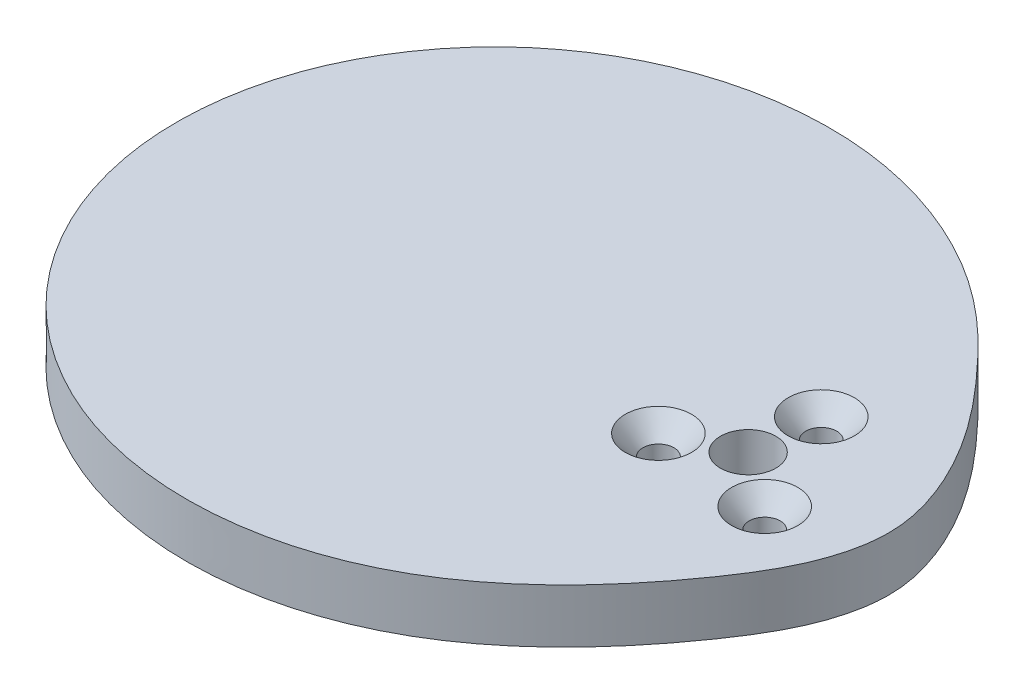
SolidWorks part; units mm, degrees
material "AISI 303 Stainless"
ref_plane "Front Plane" through (0, 0, 0) normal (0, 0, 1) x (1, 0, 0)
ref_plane "Top Plane" through (0, 0, 0) normal (0, 1, 0) x (1, 0, 0)
ref_plane "Right Plane" through (0, 0, 0) normal (1, 0, 0) x (0, 0, -1)
other "Configuration Table"
sketch "Generated Profile" plane through (0, 0, 0) normal (0, 1, 0) x (1, 0, 0)
  line L0 (0, 0) -> (25.4, 0) construction
  arc A0 (16.51, 0) -> (16.5074, 0.2882) centre (-1.1956, -0.0156) ccw
  arc A1 (16.5074, 0.2882) -> (16.4999, 0.5764) centre (-0.0271, -0.0004) ccw
  arc A2 (16.4999, 0.5764) -> (16.4873, 0.8647) centre (-0.0737, -0.0021) ccw
  arc A3 (16.4873, 0.8647) -> (16.4697, 1.1532) centre (-0.1437, -0.0058) ccw
  arc A4 (16.4697, 1.1532) -> (16.447, 1.4419) centre (-0.2374, -0.0123) ccw
  arc A5 (16.447, 1.4419) -> (16.4193, 1.7309) centre (-0.3551, -0.0226) ccw
  arc A6 (16.4193, 1.7309) -> (16.3866, 2.0202) centre (-0.4972, -0.0375) ccw
  arc A7 (16.3866, 2.0202) -> (16.3488, 2.3099) centre (-0.6642, -0.0579) ccw
  arc A8 (16.3488, 2.3099) -> (16.3059, 2.6) centre (-0.8568, -0.0847) ccw
  arc A9 (16.3059, 2.6) -> (16.2579, 2.8906) centre (-1.0754, -0.1189) ccw
  arc A10 (16.2579, 2.8906) -> (16.2049, 3.1817) centre (-1.3211, -0.1616) ccw
  arc A11 (16.2049, 3.1817) -> (16.1468, 3.4735) centre (-1.5945, -0.2138) ccw
  arc A12 (16.1468, 3.4735) -> (16.0835, 3.7658) centre (-1.8967, -0.2766) ccw
  arc A13 (16.0835, 3.7658) -> (16.0151, 4.0589) centre (-2.2288, -0.3513) ccw
  arc A14 (16.0151, 4.0589) -> (15.9416, 4.3528) centre (-2.592, -0.4391) ccw
  arc A15 (15.9416, 4.3528) -> (15.863, 4.6474) centre (-2.9877, -0.5415) ccw
  arc A16 (15.863, 4.6474) -> (15.7792, 4.9429) centre (-3.4174, -0.6598) ccw
  arc A17 (15.7792, 4.9429) -> (15.6903, 5.2394) centre (-3.8827, -0.7956) ccw
  arc A18 (15.6903, 5.2394) -> (15.5961, 5.5368) centre (-4.3854, -0.9506) ccw
  arc A19 (15.5961, 5.5368) -> (15.4968, 5.8352) centre (-4.9275, -1.1266) ccw
  arc A20 (15.4968, 5.8352) -> (15.3923, 6.1348) centre (-5.5111, -1.3256) ccw
  arc A21 (15.3923, 6.1348) -> (15.2826, 6.4355) centre (-6.1385, -1.5495) ccw
  arc A22 (15.2826, 6.4355) -> (15.1677, 6.7373) centre (-6.8121, -1.8006) ccw
  arc A23 (15.1677, 6.7373) -> (15.0476, 7.0405) centre (-7.5347, -2.0813) ccw
  arc A24 (15.0476, 7.0405) -> (14.9223, 7.3449) centre (-8.3091, -2.3941) ccw
  arc A25 (14.9223, 7.3449) -> (14.7918, 7.6508) centre (-9.1382, -2.7417) ccw
  arc A26 (14.7918, 7.6508) -> (14.6561, 7.958) centre (-10.0253, -3.127) ccw
  arc A27 (14.6561, 7.958) -> (14.5152, 8.2667) centre (-10.9736, -3.5529) ccw
  arc A28 (14.5152, 8.2667) -> (14.3691, 8.577) centre (-11.9865, -4.0226) ccw
  arc A29 (14.3691, 8.577) -> (14.2179, 8.8889) centre (-13.0674, -4.5394) ccw
  arc A30 (14.2179, 8.8889) -> (14.0614, 9.2024) centre (-14.2199, -5.1066) ccw
  arc A31 (14.0614, 9.2024) -> (13.8998, 9.5176) centre (-15.4473, -5.7275) ccw
  arc A32 (13.8998, 9.5176) -> (13.7331, 9.8345) centre (-16.7527, -6.4056) ccw
  arc A33 (13.7331, 9.8345) -> (13.5612, 10.1532) centre (-18.1389, -7.1441) ccw
  arc A34 (13.5612, 10.1532) -> (13.3843, 10.4738) centre (-19.6082, -7.9458) ccw
  arc A35 (13.3843, 10.4738) -> (13.2023, 10.7963) centre (-21.1622, -8.8133) ccw
  arc A36 (13.2023, 10.7963) -> (13.0152, 11.1207) centre (-22.8013, -9.7486) ccw
  arc A37 (13.0152, 11.1207) -> (12.8231, 11.4471) centre (-24.5248, -10.7528) ccw
  arc A38 (12.8231, 11.4471) -> (12.626, 11.7755) centre (-26.3302, -11.826) ccw
  arc A39 (12.626, 11.7755) -> (12.424, 12.1059) centre (-28.213, -12.9666) ccw
  arc A40 (12.424, 12.1059) -> (12.217, 12.4384) centre (-30.1663, -14.1717) ccw
  arc A41 (12.217, 12.4384) -> (12.0052, 12.773) centre (-32.1801, -15.436) ccw
  arc A42 (12.0052, 12.773) -> (11.7885, 13.1098) centre (-34.2413, -16.7518) ccw
  arc A43 (11.7885, 13.1098) -> (11.567, 13.4486) centre (-36.3329, -18.1087) ccw
  arc A44 (11.567, 13.4486) -> (11.3406, 13.7896) centre (-38.4346, -19.4932) ccw
  arc A45 (11.3406, 13.7896) -> (11.1095, 14.1328) centre (-40.5219, -20.8888) ccw
  arc A46 (11.1095, 14.1328) -> (10.8736, 14.4781) centre (-42.5671, -22.2759) ccw
  arc A47 (10.8736, 14.4781) -> (10.633, 14.8256) centre (-44.5394, -23.6323) ccw
  arc A48 (10.633, 14.8256) -> (10.3877, 15.1753) centre (-46.4062, -24.9334) ccw
  arc A49 (10.3877, 15.1753) -> (10.1377, 15.5271) centre (-48.1344, -26.1537) ccw
  arc A50 (10.1377, 15.5271) -> (9.8829, 15.881) centre (-49.6916, -27.2675) ccw
  arc A51 (9.8829, 15.881) -> (9.6235, 16.2371) centre (-51.0484, -28.25) ccw
  arc A52 (9.6235, 16.2371) -> (9.3593, 16.5952) centre (-52.1797, -29.0794) ccw
  arc A53 (9.3593, 16.5952) -> (9.0903, 16.9554) centre (-53.0666, -29.7375) ccw
  arc A54 (9.0903, 16.9554) -> (8.8165, 17.3177) centre (-53.6976, -30.2113) ccw
  arc A55 (8.8165, 17.3177) -> (8.5379, 17.6819) centre (-54.0689, -30.4935) ccw
  arc A56 (8.5379, 17.6819) -> (8.2544, 18.0481) centre (-54.1853, -30.5829) ccw
  arc A57 (8.2544, 18.0481) -> (7.9659, 18.4163) centre (-54.0587, -30.4842) ccw
  arc A58 (7.9659, 18.4163) -> (7.6724, 18.7863) centre (-53.708, -30.2075) ccw
  arc A59 (7.6724, 18.7863) -> (7.3737, 19.1582) centre (-53.1569, -29.7675) ccw
  arc A60 (7.3737, 19.1582) -> (7.0697, 19.5319) centre (-52.4327, -29.182) ccw
  arc A61 (7.0697, 19.5319) -> (6.7603, 19.9073) centre (-51.5645, -28.4712) ccw
  arc A62 (6.7603, 19.9073) -> (6.4454, 20.2844) centre (-50.5819, -27.656) ccw
  arc A63 (6.4454, 20.2844) -> (6.1249, 20.6631) centre (-49.5132, -26.7575) ccw
  arc A64 (6.1249, 20.6631) -> (5.7985, 21.0433) centre (-48.3852, -25.796) ccw
  arc A65 (5.7985, 21.0433) -> (5.4661, 21.4251) centre (-47.2216, -24.7901) ccw
  arc A66 (5.4661, 21.4251) -> (5.1274, 21.8083) centre (-46.0436, -23.7567) ccw
  arc A67 (5.1274, 21.8083) -> (4.7824, 22.1927) centre (-44.8688, -22.7106) ccw
  arc A68 (4.7824, 22.1927) -> (4.4307, 22.5785) centre (-43.7119, -21.6643) ccw
  arc A69 (4.4307, 22.5785) -> (4.0722, 22.9654) centre (-42.5848, -20.6285) ccw
  arc A70 (4.0722, 22.9654) -> (3.7066, 23.3533) centre (-41.4966, -19.6117) ccw
  arc A71 (3.7066, 23.3533) -> (3.3337, 23.7422) centre (-40.454, -18.6207) ccw
  arc A72 (3.3337, 23.7422) -> (2.9533, 24.1319) centre (-39.4618, -17.6608) ccw
  arc A73 (2.9533, 24.1319) -> (2.565, 24.5222) centre (-38.5231, -16.7358) ccw
  arc A74 (2.565, 24.5222) -> (2.1686, 24.9132) centre (-37.6395, -15.8485) ccw
  arc A75 (2.1686, 24.9132) -> (1.7638, 25.3045) centre (-36.8115, -15.0007) ccw
  arc A76 (1.7638, 25.3045) -> (1.3505, 25.696) centre (-36.0388, -14.1934) ccw
  arc A77 (1.3505, 25.696) -> (0.9282, 26.0876) centre (-35.3203, -13.4268) ccw
  arc A78 (0.9282, 26.0876) -> (0.4967, 26.479) centre (-34.6543, -12.7009) ccw
  arc A79 (0.4967, 26.479) -> (0.0558, 26.87) centre (-34.0389, -12.015) ccw
  arc A80 (0.0558, 26.87) -> (-0.3948, 27.2605) centre (-33.4719, -11.3683) ccw
  arc A81 (-0.3948, 27.2605) -> (-0.8554, 27.6501) centre (-32.9508, -10.7597) ccw
  arc A82 (-0.8554, 27.6501) -> (-1.3263, 28.0387) centre (-32.473, -10.188) ccw
  arc A83 (-1.3263, 28.0387) -> (-1.8077, 28.4259) centre (-32.0361, -9.6518) ccw
  arc A84 (-1.8077, 28.4259) -> (-2.2999, 28.8114) centre (-31.6373, -9.1495) ccw
  arc A85 (-2.2999, 28.8114) -> (-2.8032, 29.195) centre (-31.2743, -8.6798) ccw
  arc A86 (-2.8032, 29.195) -> (-3.3177, 29.5763) centre (-30.9445, -8.2411) ccw
  arc A87 (-3.3177, 29.5763) -> (-3.8437, 29.955) centre (-30.6455, -7.8319) ccw
  arc A88 (-3.8437, 29.955) -> (-4.3815, 30.3306) centre (-30.375, -7.4506) ccw
  arc A89 (-4.3815, 30.3306) -> (-4.9312, 30.7029) centre (-30.1309, -7.0958) ccw
  arc A90 (-4.9312, 30.7029) -> (-5.493, 31.0715) centre (-29.911, -6.7659) ccw
  arc A91 (-5.493, 31.0715) -> (-6.0672, 31.4358) centre (-29.7134, -6.4597) ccw
  arc A92 (-6.0672, 31.4358) -> (-6.6538, 31.7956) centre (-29.5361, -6.1757) ccw
  arc A93 (-6.6538, 31.7956) -> (-7.253, 32.1503) centre (-29.3775, -5.9126) ccw
  arc A94 (-7.253, 32.1503) -> (-7.865, 32.4994) centre (-29.2359, -5.669) ccw
  arc A95 (-7.865, 32.4994) -> (-8.4898, 32.8426) centre (-29.1098, -5.4437) ccw
  arc A96 (-8.4898, 32.8426) -> (-9.1276, 33.1792) centre (-28.9976, -5.2355) ccw
  arc A97 (-9.1276, 33.1792) -> (-9.7784, 33.5089) centre (-28.8982, -5.0433) ccw
  arc A98 (-9.7784, 33.5089) -> (-10.4423, 33.8311) centre (-28.8102, -4.8659) ccw
  arc A99 (-10.4423, 33.8311) -> (-11.1193, 34.1451) centre (-28.7324, -4.7022) ccw
  arc A100 (-11.1193, 34.1451) -> (-11.8093, 34.4506) centre (-28.664, -4.5512) ccw
  arc A101 (-11.8093, 34.4506) -> (-12.5124, 34.747) centre (-28.6038, -4.4119) ccw
  arc A102 (-12.5124, 34.747) -> (-13.2285, 35.0336) centre (-28.551, -4.2834) ccw
  arc A103 (-13.2285, 35.0336) -> (-13.9575, 35.31) centre (-28.5047, -4.1647) ccw
  arc A104 (-13.9575, 35.31) -> (-14.6994, 35.5755) centre (-28.4642, -4.055) ccw
  arc A105 (-14.6994, 35.5755) -> (-15.4539, 35.8296) centre (-28.429, -3.9534) ccw
  arc A106 (-15.4539, 35.8296) -> (-16.221, 36.0716) centre (-28.3982, -3.8591) ccw
  arc A107 (-16.221, 36.0716) -> (-17.0005, 36.301) centre (-28.3714, -3.7714) ccw
  arc A108 (-17.0005, 36.301) -> (-17.7921, 36.5172) centre (-28.3482, -3.6895) ccw
  arc A109 (-17.7921, 36.5172) -> (-18.5956, 36.7196) centre (-28.328, -3.6127) ccw
  arc A110 (-18.5956, 36.7196) -> (-19.4107, 36.9076) centre (-28.3106, -3.5405) ccw
  arc A111 (-19.4107, 36.9076) -> (-20.2371, 37.0806) centre (-28.2955, -3.472) ccw
  arc A112 (-20.2371, 37.0806) -> (-21.0745, 37.2381) centre (-28.2826, -3.4069) ccw
  arc A113 (-21.0745, 37.2381) -> (-21.9226, 37.3794) centre (-28.2715, -3.3445) ccw
  arc A114 (-21.9226, 37.3794) -> (-22.7809, 37.5039) centre (-28.2621, -3.2843) ccw
  arc A115 (-22.7809, 37.5039) -> (-23.649, 37.6112) centre (-28.2543, -3.2258) ccw
  arc A116 (-23.649, 37.6112) -> (-24.5265, 37.7006) centre (-28.2478, -3.1686) ccw
  arc A117 (-24.5265, 37.7006) -> (-25.4129, 37.7716) centre (-28.2427, -3.1123) ccw
  arc A118 (-25.4129, 37.7716) -> (-26.3078, 37.8237) centre (-28.2388, -3.0565) ccw
  arc A119 (-26.3078, 37.8237) -> (-27.2105, 37.8564) centre (-28.2362, -3.0008) ccw
  arc A120 (-27.2105, 37.8564) -> (-28.1205, 37.8691) centre (-28.2348, -2.9449) ccw
  arc A121 (-28.1205, 37.8691) -> (-29.0373, 37.8613) centre (-28.2346, -2.8887) ccw
  arc A122 (-29.0373, 37.8613) -> (-29.9602, 37.8327) centre (-28.2358, -2.8317) ccw
  arc A123 (-29.9602, 37.8327) -> (-30.8886, 37.7827) centre (-28.2382, -2.7738) ccw
  arc A124 (-30.8886, 37.7827) -> (-31.8218, 37.7109) centre (-28.2421, -2.7149) ccw
  arc A125 (-31.8218, 37.7109) -> (-32.7592, 37.6169) centre (-28.2474, -2.6548) ccw
  arc A126 (-32.7592, 37.6169) -> (-33.7001, 37.5003) centre (-28.2543, -2.5933) ccw
  arc A127 (-33.7001, 37.5003) -> (-34.6437, 37.3607) centre (-28.2628, -2.5304) ccw
  arc A128 (-34.6437, 37.3607) -> (-35.5892, 37.1979) centre (-28.2731, -2.466) ccw
  arc A129 (-35.5892, 37.1979) -> (-36.536, 37.0115) centre (-28.2853, -2.4001) ccw
  arc A130 (-36.536, 37.0115) -> (-37.4833, 36.8013) centre (-28.2994, -2.3327) ccw
  arc A131 (-37.4833, 36.8013) -> (-38.4302, 36.5669) centre (-28.3156, -2.2638) ccw
  arc A132 (-38.4302, 36.5669) -> (-39.3759, 36.3081) centre (-28.3339, -2.1934) ccw
  arc A133 (-39.3759, 36.3081) -> (-40.3196, 36.0249) centre (-28.3545, -2.1217) ccw
  arc A134 (-40.3196, 36.0249) -> (-41.2605, 35.7169) centre (-28.3774, -2.0487) ccw
  arc A135 (-41.2605, 35.7169) -> (-42.1977, 35.384) centre (-28.4027, -1.9745) ccw
  arc A136 (-42.1977, 35.384) -> (-43.1303, 35.0263) centre (-28.4305, -1.8993) ccw
  arc A137 (-43.1303, 35.0263) -> (-44.0575, 34.6435) centre (-28.4608, -1.8233) ccw
  arc A138 (-44.0575, 34.6435) -> (-44.9784, 34.2357) centre (-28.4936, -1.7465) ccw
  arc A139 (-44.9784, 34.2357) -> (-45.8921, 33.8029) centre (-28.529, -1.6692) ccw
  arc A140 (-45.8921, 33.8029) -> (-46.7977, 33.345) centre (-28.567, -1.5915) ccw
  arc A141 (-46.7977, 33.345) -> (-47.6944, 32.8623) centre (-28.6076, -1.5138) ccw
  arc A142 (-47.6944, 32.8623) -> (-48.5812, 32.3547) centre (-28.6507, -1.4361) ccw
  arc A143 (-48.5812, 32.3547) -> (-49.4572, 31.8224) centre (-28.6964, -1.3587) ccw
  arc A144 (-49.4572, 31.8224) -> (-50.3216, 31.2656) centre (-28.7445, -1.2818) ccw
  arc A145 (-50.3216, 31.2656) -> (-51.1735, 30.6844) centre (-28.795, -1.2057) ccw
  arc A146 (-51.1735, 30.6844) -> (-52.012, 30.0792) centre (-28.8477, -1.1305) ccw
  arc A147 (-52.012, 30.0792) -> (-52.8362, 29.4502) centre (-28.9026, -1.0565) ccw
  arc A148 (-52.8362, 29.4502) -> (-53.6452, 28.7978) centre (-28.9596, -0.984) ccw
  arc A149 (-53.6452, 28.7978) -> (-54.4383, 28.1221) centre (-29.0183, -0.913) ccw
  arc A150 (-54.4383, 28.1221) -> (-55.2145, 27.4238) centre (-29.0788, -0.8439) ccw
  arc A151 (-55.2145, 27.4238) -> (-55.973, 26.703) centre (-29.1409, -0.7769) ccw
  arc A152 (-55.973, 26.703) -> (-56.7131, 25.9604) centre (-29.2042, -0.712) ccw
  arc A153 (-56.7131, 25.9604) -> (-57.4338, 25.1963) centre (-29.2686, -0.6496) ccw
  arc A154 (-57.4338, 25.1963) -> (-58.1344, 24.4114) centre (-29.3339, -0.5896) ccw
  arc A155 (-58.1344, 24.4114) -> (-58.8142, 23.606) centre (-29.3998, -0.5324) ccw
  arc A156 (-58.8142, 23.606) -> (-59.4724, 22.7808) centre (-29.4661, -0.478) ccw
  arc A157 (-59.4724, 22.7808) -> (-60.1083, 21.9363) centre (-29.5325, -0.4266) ccw
  arc A158 (-60.1083, 21.9363) -> (-60.7212, 21.0733) centre (-29.5987, -0.3781) ccw
  arc A159 (-60.7212, 21.0733) -> (-61.3103, 20.1923) centre (-29.6645, -0.3328) ccw
  arc A160 (-61.3103, 20.1923) -> (-61.8751, 19.2941) centre (-29.7295, -0.2906) ccw
  arc A161 (-61.8751, 19.2941) -> (-62.4149, 18.3792) centre (-29.7936, -0.2516) ccw
  arc A162 (-62.4149, 18.3792) -> (-62.929, 17.4486) centre (-29.8563, -0.2157) ccw
  arc A163 (-62.929, 17.4486) -> (-63.417, 16.5028) centre (-29.9175, -0.1831) ccw
  arc A164 (-63.417, 16.5028) -> (-63.8783, 15.5427) centre (-29.9768, -0.1535) ccw
  arc A165 (-63.8783, 15.5427) -> (-64.3123, 14.569) centre (-30.0339, -0.1271) ccw
  arc A166 (-64.3123, 14.569) -> (-64.7185, 13.5827) centre (-30.0886, -0.1036) ccw
  arc A167 (-64.7185, 13.5827) -> (-65.0966, 12.5845) centre (-30.1407, -0.083) ccw
  arc A168 (-65.0966, 12.5845) -> (-65.446, 11.5752) centre (-30.1898, -0.0652) ccw
  arc A169 (-65.446, 11.5752) -> (-65.7664, 10.5557) centre (-30.2358, -0.05) ccw
  arc A170 (-65.7664, 10.5557) -> (-66.0573, 9.5269) centre (-30.2783, -0.0373) ccw
  arc A171 (-66.0573, 9.5269) -> (-66.3186, 8.4898) centre (-30.3172, -0.0269) ccw
  arc A172 (-66.3186, 8.4898) -> (-66.5498, 7.4451) centre (-30.3524, -0.0186) ccw
  arc A173 (-66.5498, 7.4451) -> (-66.7507, 6.3938) centre (-30.3835, -0.0122) ccw
  arc A174 (-66.7507, 6.3938) -> (-66.9211, 5.3369) centre (-30.4105, -0.0074) ccw
  arc A175 (-66.9211, 5.3369) -> (-67.0608, 4.2752) centre (-30.4332, -0.0041) ccw
  arc A176 (-67.0608, 4.2752) -> (-67.1696, 3.2097) centre (-30.4515, -0.0019) ccw
  arc A177 (-67.1696, 3.2097) -> (-67.2475, 2.1414) centre (-30.4653, -0.0007) ccw
  arc A178 (-67.2475, 2.1414) -> (-67.2942, 1.0712) centre (-30.4746, -0.0001) ccw
  arc A179 (-67.2942, 1.0712) -> (-67.31, 0) centre (-29.3336, -0.025) ccw
  arc A180 (-67.31, 0) -> (-67.2942, -1.0712) centre (-29.3336, 0.025) ccw
  arc A181 (-67.2942, -1.0712) -> (-67.2475, -2.1414) centre (-30.4746, 0.0001) ccw
  arc A182 (-67.2475, -2.1414) -> (-67.1696, -3.2097) centre (-30.4653, 0.0007) ccw
  arc A183 (-67.1696, -3.2097) -> (-67.0608, -4.2752) centre (-30.4515, 0.0019) ccw
  arc A184 (-67.0608, -4.2752) -> (-66.9211, -5.3369) centre (-30.4332, 0.0041) ccw
  arc A185 (-66.9211, -5.3369) -> (-66.7507, -6.3938) centre (-30.4105, 0.0074) ccw
  arc A186 (-66.7507, -6.3938) -> (-66.5498, -7.4451) centre (-30.3835, 0.0122) ccw
  arc A187 (-66.5498, -7.4451) -> (-66.3186, -8.4898) centre (-30.3524, 0.0186) ccw
  arc A188 (-66.3186, -8.4898) -> (-66.0573, -9.5269) centre (-30.3172, 0.0269) ccw
  arc A189 (-66.0573, -9.5269) -> (-65.7664, -10.5557) centre (-30.2783, 0.0373) ccw
  arc A190 (-65.7664, -10.5557) -> (-65.446, -11.5752) centre (-30.2358, 0.05) ccw
  arc A191 (-65.446, -11.5752) -> (-65.0966, -12.5845) centre (-30.1898, 0.0652) ccw
  arc A192 (-65.0966, -12.5845) -> (-64.7185, -13.5827) centre (-30.1407, 0.083) ccw
  arc A193 (-64.7185, -13.5827) -> (-64.3123, -14.569) centre (-30.0886, 0.1036) ccw
  arc A194 (-64.3123, -14.569) -> (-63.8783, -15.5427) centre (-30.0339, 0.1271) ccw
  arc A195 (-63.8783, -15.5427) -> (-63.417, -16.5028) centre (-29.9768, 0.1535) ccw
  arc A196 (-63.417, -16.5028) -> (-62.929, -17.4486) centre (-29.9175, 0.1831) ccw
  arc A197 (-62.929, -17.4486) -> (-62.4149, -18.3792) centre (-29.8563, 0.2157) ccw
  arc A198 (-62.4149, -18.3792) -> (-61.8751, -19.2941) centre (-29.7936, 0.2516) ccw
  arc A199 (-61.8751, -19.2941) -> (-61.3103, -20.1923) centre (-29.7295, 0.2906) ccw
  arc A200 (-61.3103, -20.1923) -> (-60.7212, -21.0733) centre (-29.6645, 0.3328) ccw
  arc A201 (-60.7212, -21.0733) -> (-60.1083, -21.9363) centre (-29.5987, 0.3781) ccw
  arc A202 (-60.1083, -21.9363) -> (-59.4724, -22.7808) centre (-29.5325, 0.4266) ccw
  arc A203 (-59.4724, -22.7808) -> (-58.8142, -23.606) centre (-29.4661, 0.478) ccw
  arc A204 (-58.8142, -23.606) -> (-58.1344, -24.4114) centre (-29.3998, 0.5324) ccw
  arc A205 (-58.1344, -24.4114) -> (-57.4338, -25.1963) centre (-29.3339, 0.5896) ccw
  arc A206 (-57.4338, -25.1963) -> (-56.7131, -25.9604) centre (-29.2686, 0.6496) ccw
  arc A207 (-56.7131, -25.9604) -> (-55.973, -26.703) centre (-29.2042, 0.712) ccw
  arc A208 (-55.973, -26.703) -> (-55.2145, -27.4238) centre (-29.1409, 0.7769) ccw
  arc A209 (-55.2145, -27.4238) -> (-54.4383, -28.1221) centre (-29.0788, 0.8439) ccw
  arc A210 (-54.4383, -28.1221) -> (-53.6452, -28.7978) centre (-29.0183, 0.913) ccw
  arc A211 (-53.6452, -28.7978) -> (-52.8362, -29.4502) centre (-28.9596, 0.984) ccw
  arc A212 (-52.8362, -29.4502) -> (-52.012, -30.0792) centre (-28.9026, 1.0565) ccw
  arc A213 (-52.012, -30.0792) -> (-51.1735, -30.6844) centre (-28.8477, 1.1305) ccw
  arc A214 (-51.1735, -30.6844) -> (-50.3216, -31.2656) centre (-28.795, 1.2057) ccw
  arc A215 (-50.3216, -31.2656) -> (-49.4572, -31.8224) centre (-28.7445, 1.2818) ccw
  arc A216 (-49.4572, -31.8224) -> (-48.5812, -32.3547) centre (-28.6964, 1.3587) ccw
  arc A217 (-48.5812, -32.3547) -> (-47.6944, -32.8623) centre (-28.6507, 1.4361) ccw
  arc A218 (-47.6944, -32.8623) -> (-46.7977, -33.345) centre (-28.6076, 1.5138) ccw
  arc A219 (-46.7977, -33.345) -> (-45.8921, -33.8029) centre (-28.567, 1.5915) ccw
  arc A220 (-45.8921, -33.8029) -> (-44.9784, -34.2357) centre (-28.529, 1.6692) ccw
  arc A221 (-44.9784, -34.2357) -> (-44.0575, -34.6435) centre (-28.4936, 1.7465) ccw
  arc A222 (-44.0575, -34.6435) -> (-43.1303, -35.0263) centre (-28.4608, 1.8233) ccw
  arc A223 (-43.1303, -35.0263) -> (-42.1977, -35.384) centre (-28.4305, 1.8993) ccw
  arc A224 (-42.1977, -35.384) -> (-41.2605, -35.7169) centre (-28.4027, 1.9745) ccw
  arc A225 (-41.2605, -35.7169) -> (-40.3196, -36.0249) centre (-28.3774, 2.0487) ccw
  arc A226 (-40.3196, -36.0249) -> (-39.3759, -36.3081) centre (-28.3545, 2.1217) ccw
  arc A227 (-39.3759, -36.3081) -> (-38.4302, -36.5669) centre (-28.3339, 2.1934) ccw
  arc A228 (-38.4302, -36.5669) -> (-37.4833, -36.8013) centre (-28.3156, 2.2638) ccw
  arc A229 (-37.4833, -36.8013) -> (-36.536, -37.0115) centre (-28.2994, 2.3327) ccw
  arc A230 (-36.536, -37.0115) -> (-35.5892, -37.1979) centre (-28.2853, 2.4001) ccw
  arc A231 (-35.5892, -37.1979) -> (-34.6437, -37.3607) centre (-28.2731, 2.466) ccw
  arc A232 (-34.6437, -37.3607) -> (-33.7001, -37.5003) centre (-28.2628, 2.5304) ccw
  arc A233 (-33.7001, -37.5003) -> (-32.7592, -37.6169) centre (-28.2543, 2.5933) ccw
  arc A234 (-32.7592, -37.6169) -> (-31.8218, -37.7109) centre (-28.2474, 2.6548) ccw
  arc A235 (-31.8218, -37.7109) -> (-30.8886, -37.7827) centre (-28.2421, 2.7149) ccw
  arc A236 (-30.8886, -37.7827) -> (-29.9602, -37.8327) centre (-28.2382, 2.7738) ccw
  arc A237 (-29.9602, -37.8327) -> (-29.0373, -37.8613) centre (-28.2358, 2.8317) ccw
  arc A238 (-29.0373, -37.8613) -> (-28.1205, -37.8691) centre (-28.2346, 2.8887) ccw
  arc A239 (-28.1205, -37.8691) -> (-27.2105, -37.8564) centre (-28.2348, 2.9449) ccw
  arc A240 (-27.2105, -37.8564) -> (-26.3078, -37.8237) centre (-28.2362, 3.0008) ccw
  arc A241 (-26.3078, -37.8237) -> (-25.4129, -37.7716) centre (-28.2388, 3.0565) ccw
  arc A242 (-25.4129, -37.7716) -> (-24.5265, -37.7006) centre (-28.2427, 3.1123) ccw
  arc A243 (-24.5265, -37.7006) -> (-23.649, -37.6112) centre (-28.2478, 3.1686) ccw
  arc A244 (-23.649, -37.6112) -> (-22.7809, -37.5039) centre (-28.2543, 3.2258) ccw
  arc A245 (-22.7809, -37.5039) -> (-21.9226, -37.3794) centre (-28.2621, 3.2843) ccw
  arc A246 (-21.9226, -37.3794) -> (-21.0745, -37.2381) centre (-28.2715, 3.3445) ccw
  arc A247 (-21.0745, -37.2381) -> (-20.2371, -37.0806) centre (-28.2826, 3.4069) ccw
  arc A248 (-20.2371, -37.0806) -> (-19.4107, -36.9076) centre (-28.2955, 3.472) ccw
  arc A249 (-19.4107, -36.9076) -> (-18.5956, -36.7196) centre (-28.3106, 3.5405) ccw
  arc A250 (-18.5956, -36.7196) -> (-17.7921, -36.5172) centre (-28.328, 3.6127) ccw
  arc A251 (-17.7921, -36.5172) -> (-17.0005, -36.301) centre (-28.3482, 3.6895) ccw
  arc A252 (-17.0005, -36.301) -> (-16.221, -36.0716) centre (-28.3714, 3.7714) ccw
  arc A253 (-16.221, -36.0716) -> (-15.4539, -35.8296) centre (-28.3982, 3.8591) ccw
  arc A254 (-15.4539, -35.8296) -> (-14.6994, -35.5755) centre (-28.429, 3.9534) ccw
  arc A255 (-14.6994, -35.5755) -> (-13.9575, -35.31) centre (-28.4642, 4.055) ccw
  arc A256 (-13.9575, -35.31) -> (-13.2285, -35.0336) centre (-28.5047, 4.1647) ccw
  arc A257 (-13.2285, -35.0336) -> (-12.5124, -34.747) centre (-28.551, 4.2834) ccw
  arc A258 (-12.5124, -34.747) -> (-11.8093, -34.4506) centre (-28.6038, 4.4119) ccw
  arc A259 (-11.8093, -34.4506) -> (-11.1193, -34.1451) centre (-28.664, 4.5512) ccw
  arc A260 (-11.1193, -34.1451) -> (-10.4423, -33.8311) centre (-28.7324, 4.7022) ccw
  arc A261 (-10.4423, -33.8311) -> (-9.7784, -33.5089) centre (-28.8102, 4.8659) ccw
  arc A262 (-9.7784, -33.5089) -> (-9.1276, -33.1792) centre (-28.8982, 5.0433) ccw
  arc A263 (-9.1276, -33.1792) -> (-8.4898, -32.8426) centre (-28.9976, 5.2355) ccw
  arc A264 (-8.4898, -32.8426) -> (-7.865, -32.4994) centre (-29.1098, 5.4437) ccw
  arc A265 (-7.865, -32.4994) -> (-7.253, -32.1503) centre (-29.2359, 5.669) ccw
  arc A266 (-7.253, -32.1503) -> (-6.6538, -31.7956) centre (-29.3775, 5.9126) ccw
  arc A267 (-6.6538, -31.7956) -> (-6.0672, -31.4358) centre (-29.5361, 6.1757) ccw
  arc A268 (-6.0672, -31.4358) -> (-5.493, -31.0715) centre (-29.7134, 6.4597) ccw
  arc A269 (-5.493, -31.0715) -> (-4.9312, -30.7029) centre (-29.911, 6.7659) ccw
  arc A270 (-4.9312, -30.7029) -> (-4.3815, -30.3306) centre (-30.1309, 7.0958) ccw
  arc A271 (-4.3815, -30.3306) -> (-3.8437, -29.955) centre (-30.375, 7.4506) ccw
  arc A272 (-3.8437, -29.955) -> (-3.3177, -29.5763) centre (-30.6455, 7.8319) ccw
  arc A273 (-3.3177, -29.5763) -> (-2.8032, -29.195) centre (-30.9445, 8.2411) ccw
  arc A274 (-2.8032, -29.195) -> (-2.2999, -28.8114) centre (-31.2743, 8.6798) ccw
  arc A275 (-2.2999, -28.8114) -> (-1.8077, -28.4259) centre (-31.6373, 9.1495) ccw
  arc A276 (-1.8077, -28.4259) -> (-1.3263, -28.0387) centre (-32.0361, 9.6518) ccw
  arc A277 (-1.3263, -28.0387) -> (-0.8554, -27.6501) centre (-32.473, 10.188) ccw
  arc A278 (-0.8554, -27.6501) -> (-0.3948, -27.2605) centre (-32.9508, 10.7597) ccw
  arc A279 (-0.3948, -27.2605) -> (0.0558, -26.87) centre (-33.4719, 11.3683) ccw
  arc A280 (0.0558, -26.87) -> (0.4967, -26.479) centre (-34.0389, 12.015) ccw
  arc A281 (0.4967, -26.479) -> (0.9282, -26.0876) centre (-34.6543, 12.7009) ccw
  arc A282 (0.9282, -26.0876) -> (1.3505, -25.696) centre (-35.3203, 13.4268) ccw
  arc A283 (1.3505, -25.696) -> (1.7638, -25.3045) centre (-36.0388, 14.1934) ccw
  arc A284 (1.7638, -25.3045) -> (2.1686, -24.9132) centre (-36.8115, 15.0007) ccw
  arc A285 (2.1686, -24.9132) -> (2.565, -24.5222) centre (-37.6395, 15.8485) ccw
  arc A286 (2.565, -24.5222) -> (2.9533, -24.1319) centre (-38.5231, 16.7358) ccw
  arc A287 (2.9533, -24.1319) -> (3.3337, -23.7422) centre (-39.4618, 17.6608) ccw
  arc A288 (3.3337, -23.7422) -> (3.7066, -23.3533) centre (-40.454, 18.6207) ccw
  arc A289 (3.7066, -23.3533) -> (4.0722, -22.9654) centre (-41.4966, 19.6117) ccw
  arc A290 (4.0722, -22.9654) -> (4.4307, -22.5785) centre (-42.5848, 20.6285) ccw
  arc A291 (4.4307, -22.5785) -> (4.7824, -22.1927) centre (-43.7119, 21.6643) ccw
  arc A292 (4.7824, -22.1927) -> (5.1274, -21.8083) centre (-44.8688, 22.7106) ccw
  arc A293 (5.1274, -21.8083) -> (5.4661, -21.4251) centre (-46.0436, 23.7567) ccw
  arc A294 (5.4661, -21.4251) -> (5.7985, -21.0433) centre (-47.2216, 24.7901) ccw
  arc A295 (5.7985, -21.0433) -> (6.1249, -20.6631) centre (-48.3852, 25.796) ccw
  arc A296 (6.1249, -20.6631) -> (6.4454, -20.2844) centre (-49.5132, 26.7575) ccw
  arc A297 (6.4454, -20.2844) -> (6.7603, -19.9073) centre (-50.5819, 27.656) ccw
  arc A298 (6.7603, -19.9073) -> (7.0697, -19.5319) centre (-51.5645, 28.4712) ccw
  arc A299 (7.0697, -19.5319) -> (7.3737, -19.1582) centre (-52.4327, 29.182) ccw
  arc A300 (7.3737, -19.1582) -> (7.6724, -18.7863) centre (-53.1569, 29.7675) ccw
  arc A301 (7.6724, -18.7863) -> (7.9659, -18.4163) centre (-53.708, 30.2075) ccw
  arc A302 (7.9659, -18.4163) -> (8.2544, -18.0481) centre (-54.0587, 30.4842) ccw
  arc A303 (8.2544, -18.0481) -> (8.5379, -17.6819) centre (-54.1853, 30.5829) ccw
  arc A304 (8.5379, -17.6819) -> (8.8165, -17.3177) centre (-54.0689, 30.4935) ccw
  arc A305 (8.8165, -17.3177) -> (9.0903, -16.9554) centre (-53.6976, 30.2113) ccw
  arc A306 (9.0903, -16.9554) -> (9.3593, -16.5952) centre (-53.0666, 29.7375) ccw
  arc A307 (9.3593, -16.5952) -> (9.6235, -16.2371) centre (-52.1797, 29.0794) ccw
  arc A308 (9.6235, -16.2371) -> (9.8829, -15.881) centre (-51.0484, 28.25) ccw
  arc A309 (9.8829, -15.881) -> (10.1377, -15.5271) centre (-49.6916, 27.2675) ccw
  arc A310 (10.1377, -15.5271) -> (10.3877, -15.1753) centre (-48.1344, 26.1537) ccw
  arc A311 (10.3877, -15.1753) -> (10.633, -14.8256) centre (-46.4062, 24.9334) ccw
  arc A312 (10.633, -14.8256) -> (10.8736, -14.4781) centre (-44.5394, 23.6323) ccw
  arc A313 (10.8736, -14.4781) -> (11.1095, -14.1328) centre (-42.5671, 22.2759) ccw
  arc A314 (11.1095, -14.1328) -> (11.3406, -13.7896) centre (-40.5219, 20.8888) ccw
  arc A315 (11.3406, -13.7896) -> (11.567, -13.4486) centre (-38.4346, 19.4932) ccw
  arc A316 (11.567, -13.4486) -> (11.7885, -13.1098) centre (-36.3329, 18.1087) ccw
  arc A317 (11.7885, -13.1098) -> (12.0052, -12.773) centre (-34.2413, 16.7518) ccw
  arc A318 (12.0052, -12.773) -> (12.217, -12.4384) centre (-32.1801, 15.436) ccw
  arc A319 (12.217, -12.4384) -> (12.424, -12.1059) centre (-30.1663, 14.1717) ccw
  arc A320 (12.424, -12.1059) -> (12.626, -11.7755) centre (-28.213, 12.9666) ccw
  arc A321 (12.626, -11.7755) -> (12.8231, -11.4471) centre (-26.3302, 11.826) ccw
  arc A322 (12.8231, -11.4471) -> (13.0152, -11.1207) centre (-24.5248, 10.7528) ccw
  arc A323 (13.0152, -11.1207) -> (13.2023, -10.7963) centre (-22.8013, 9.7486) ccw
  arc A324 (13.2023, -10.7963) -> (13.3843, -10.4738) centre (-21.1622, 8.8133) ccw
  arc A325 (13.3843, -10.4738) -> (13.5612, -10.1532) centre (-19.6082, 7.9458) ccw
  arc A326 (13.5612, -10.1532) -> (13.7331, -9.8345) centre (-18.1389, 7.1441) ccw
  arc A327 (13.7331, -9.8345) -> (13.8998, -9.5176) centre (-16.7527, 6.4056) ccw
  arc A328 (13.8998, -9.5176) -> (14.0614, -9.2024) centre (-15.4473, 5.7275) ccw
  arc A329 (14.0614, -9.2024) -> (14.2179, -8.8889) centre (-14.2199, 5.1066) ccw
  arc A330 (14.2179, -8.8889) -> (14.3691, -8.577) centre (-13.0674, 4.5394) ccw
  arc A331 (14.3691, -8.577) -> (14.5152, -8.2667) centre (-11.9865, 4.0226) ccw
  arc A332 (14.5152, -8.2667) -> (14.6561, -7.958) centre (-10.9736, 3.5529) ccw
  arc A333 (14.6561, -7.958) -> (14.7918, -7.6508) centre (-10.0253, 3.127) ccw
  arc A334 (14.7918, -7.6508) -> (14.9223, -7.3449) centre (-9.1382, 2.7417) ccw
  arc A335 (14.9223, -7.3449) -> (15.0476, -7.0405) centre (-8.3091, 2.3941) ccw
  arc A336 (15.0476, -7.0405) -> (15.1677, -6.7373) centre (-7.5347, 2.0813) ccw
  arc A337 (15.1677, -6.7373) -> (15.2826, -6.4355) centre (-6.8121, 1.8006) ccw
  arc A338 (15.2826, -6.4355) -> (15.3923, -6.1348) centre (-6.1385, 1.5495) ccw
  arc A339 (15.3923, -6.1348) -> (15.4968, -5.8352) centre (-5.5111, 1.3256) ccw
  arc A340 (15.4968, -5.8352) -> (15.5961, -5.5368) centre (-4.9275, 1.1266) ccw
  arc A341 (15.5961, -5.5368) -> (15.6903, -5.2394) centre (-4.3854, 0.9506) ccw
  arc A342 (15.6903, -5.2394) -> (15.7792, -4.9429) centre (-3.8827, 0.7956) ccw
  arc A343 (15.7792, -4.9429) -> (15.863, -4.6474) centre (-3.4174, 0.6598) ccw
  arc A344 (15.863, -4.6474) -> (15.9416, -4.3528) centre (-2.9877, 0.5415) ccw
  arc A345 (15.9416, -4.3528) -> (16.0151, -4.0589) centre (-2.592, 0.4391) ccw
  arc A346 (16.0151, -4.0589) -> (16.0835, -3.7658) centre (-2.2288, 0.3513) ccw
  arc A347 (16.0835, -3.7658) -> (16.1468, -3.4735) centre (-1.8967, 0.2766) ccw
  arc A348 (16.1468, -3.4735) -> (16.2049, -3.1817) centre (-1.5945, 0.2138) ccw
  arc A349 (16.2049, -3.1817) -> (16.2579, -2.8906) centre (-1.3211, 0.1616) ccw
  arc A350 (16.2579, -2.8906) -> (16.3059, -2.6) centre (-1.0754, 0.1189) ccw
  arc A351 (16.3059, -2.6) -> (16.3488, -2.3099) centre (-0.8568, 0.0847) ccw
  arc A352 (16.3488, -2.3099) -> (16.3866, -2.0202) centre (-0.6642, 0.0579) ccw
  arc A353 (16.3866, -2.0202) -> (16.4193, -1.7309) centre (-0.4972, 0.0375) ccw
  arc A354 (16.4193, -1.7309) -> (16.447, -1.4419) centre (-0.3551, 0.0226) ccw
  arc A355 (16.447, -1.4419) -> (16.4697, -1.1532) centre (-0.2374, 0.0123) ccw
  arc A356 (16.4697, -1.1532) -> (16.4873, -0.8647) centre (-0.1437, 0.0058) ccw
  arc A357 (16.4873, -0.8647) -> (16.4999, -0.5764) centre (-0.0737, 0.0021) ccw
  arc A358 (16.4999, -0.5764) -> (16.5074, -0.2882) centre (-0.0271, 0.0004) ccw
  arc A359 (16.5074, -0.2882) -> (16.51, 0) centre (-1.1956, 0.0156) ccw
sketch "Sketch4" plane through (0, 0, 0) normal (0, 1, 0) x (1, 0, 0)
  spline S0 degree 3 poles (15.0822, -7.9594) (16.6564, -2.148) (16.3847, 2.986) (13.9008, 11.6058) (7.811, 19.1554) (0.3979, 26.7537) (-7.9147, 33.4537) (-20.8099, 38.1868) (-34.9874, 37.8511) (-46.3267, 34.2824) (-57.678, 26.3363) (-64.5824, 15.7009) (-66.8223, 6.7582) (-67.2943, 2.1439) (-67.3459, -1.4295) (-66.7894, -7.8154) (-63.7759, -17.4159) (-55.4523, -28.4667) (-43.3405, -35.8293) (-29.5366, -38.5717) (-16.8916, -36.9328) (-5.018, -31.4823) (3.9465, -23.6477) (10.4684, -15.3398) (15.0822, -7.9594) (16.6564, -2.148) (16.3847, 2.986) knots -0.105745 -0.063745 -0.033157 0 0.007033 0.029286 0.107768 0.121104 0.158718 0.237026 0.281652 0.329526 0.37956 0.447773 0.4781 0.491134 0.504172 0.521548 0.569036 0.62446 0.686375 0.737017 0.793225 0.838519 0.894255 0.936255 0.966843 1 1.007033 1.029286 1.107768 only from (16.51, 0) to (16.51, 0)
sketch "Sketch3" plane through (0, 0, 0) normal (0, 1, 0) x (1, 0, 0)
  line L0 (0, 0) -> (0, 7.9502) construction
  line L1 (0, 0) -> (0.6929, 7.9199) construction
  circle A0 centre (0, 0) radius 7.9502 construction
  point P4 (0.6929, 7.9199)
  point P5 (6.5124, -4.56)
  point P6 (-7.2053, -3.3599)
  point P9 (0, 0)
  dimension "D1" = 15.9004
  dimension "timing" = 5
  dimension "D2" = 3
extrude "Boss-Extrude1" add sketch "Sketch4" along normal mid plane 6.35
sketch "Sketch5" plane through (0, 3.175, 0) normal (0, 1, 0) x (1, 0, 0)
  point P0 (0.6929, 7.9199)
  point P3 (6.5124, -4.56)
  point P6 (-7.2053, -3.3599)
hole_wizard "CSK for #6 Flat Head Socket Cap Screw1" positions "Sketch5" profile "Sketch6" countersink size "#6" standard "ANSI Inch" end condition through all
sketch "Sketch6" plane through (0.6929, 3.175, -7.9199) normal (1, 0, 0) x (0, 0, 1)
  line L0 (0, 0) -> (0, 6.35)
  line L1 (0, 6.35) -> (1.8288, 6.35)
  line L2 (1.8288, 6.35) -> (1.8288, 2.3814)
  line L3 (1.8288, 2.3814) -> (3.8989, 0)
  line L5 (3.8989, 0) -> (0, 0)
  line L6 (-1.8288, 2.3814) -> (-3.8989, 0) construction
  line L11 (0, -6.35) -> (0, 107.95) construction
  dimension "Thru Hole Dia." = 3.6576
  dimension "Thru Hole Depth" = 6.35
  dimension "Near C'Sink Dia." = 7.7978
  dimension "Near C'Sink Angle" = 82
sketch "Sketch7" plane through (0, 3.175, 0) normal (0, 1, 0) x (1, 0, 0)
  point P0 (0, 0)
hole_wizard "F (0.257) Diameter Hole1" positions "Sketch7" profile "Sketch8" hole size "F" standard "ANSI Inch" end condition through all
sketch "Sketch8" plane through (0, 3.175, 0) normal (1, 0, 0) x (0, 0, 1)
  line L0 (0, 0) -> (0, 6.35)
  line L1 (0, 6.35) -> (3.2639, 6.35)
  line L2 (3.2639, 6.35) -> (3.2639, 0)
  line L5 (3.2639, 0) -> (0, 0)
  line L11 (0, -6.35) -> (0, 107.95) construction
  dimension "Thru Hole Dia." = 6.5278
  dimension "Thru Hole Depth" = 6.35
